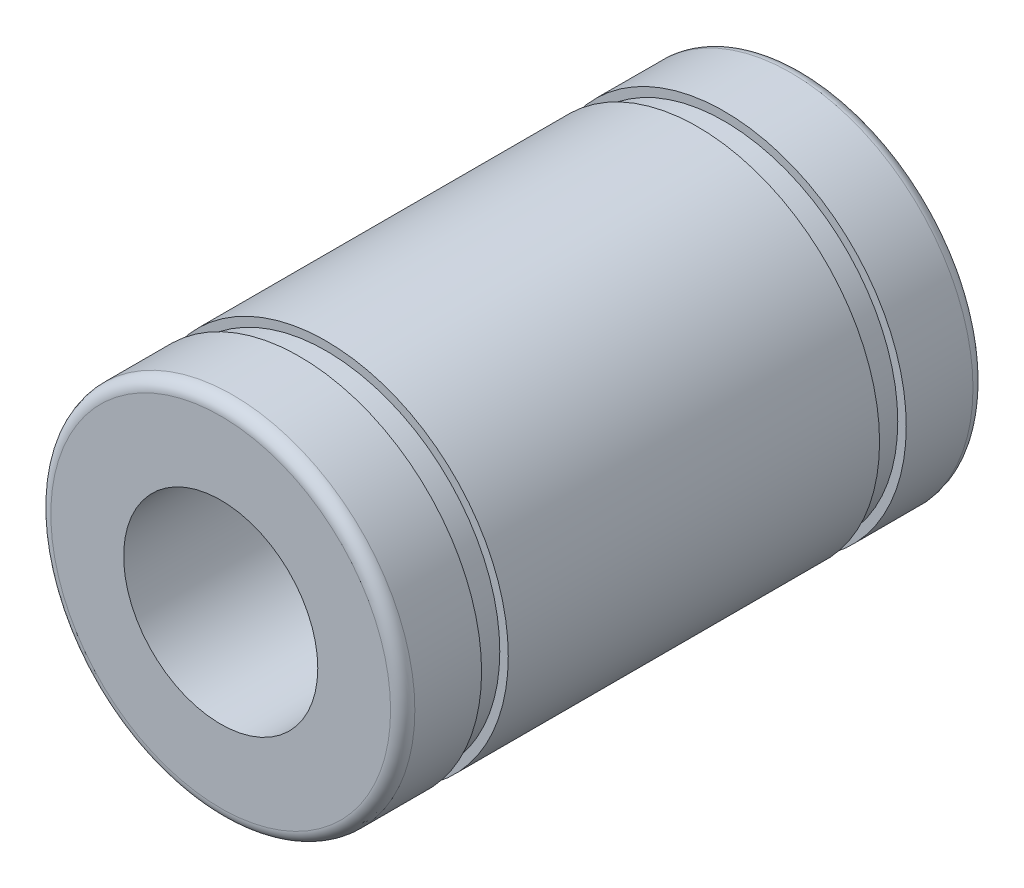
SolidWorks part; units mm, degrees
ref_plane "Front Plane" through (0, 0, 0) normal (0, 0, 1) x (1, 0, 0)
ref_plane "Top Plane" through (0, 0, 0) normal (0, 1, 0) x (1, 0, 0)
ref_plane "Right Plane" through (0, 0, 0) normal (1, 0, 0) x (0, 0, -1)
sketch "Sketch1" plane through (0, 0, 0) normal (1, 0, 0) x (0, 0, -1)
  line L0 (-1000, 0) -> (49000, 0) construction
  line L1 (-12, -7.5) -> (-8.75, -7.5)
  line L2 (-12, -7.5) -> (-12, -4)
  line L3 (0, -1000) -> (0, -4) construction
  line L4 (-7.65, -7.5) -> (-7.65, -7.15)
  line L5 (-8.75, -7.5) -> (-8.75, -7.15)
  line L6 (-8.75, -7.15) -> (-7.65, -7.15)
  line L7 (-7.65, -7.5) -> (0, -7.5)
  line L8 (-12, -4) -> (0, -4)
  line L9 (0, -4) -> (0, -7.5)
  line L10 (0, 0) -> (0, 49000) construction
  dimension "D1" = 7.5
  dimension "D2" = 12
  dimension "D3" = 8.75
  dimension "D4" = 1.1
  dimension "D5" = 7.15
  dimension "D6" = 4
revolve "Revolve1" add sketch "Sketch1" angle 360 about L0
fillet "Fillet2" radius 0.5 1 edges at (7.5, 0, 12)
mirror "Mirror2" about plane through (0, -4, 0) normal (0, 0, -1) of "Revolve1"
fillet "Fillet3" radius 0.5 1 edges at (7.5, 0, -12)
